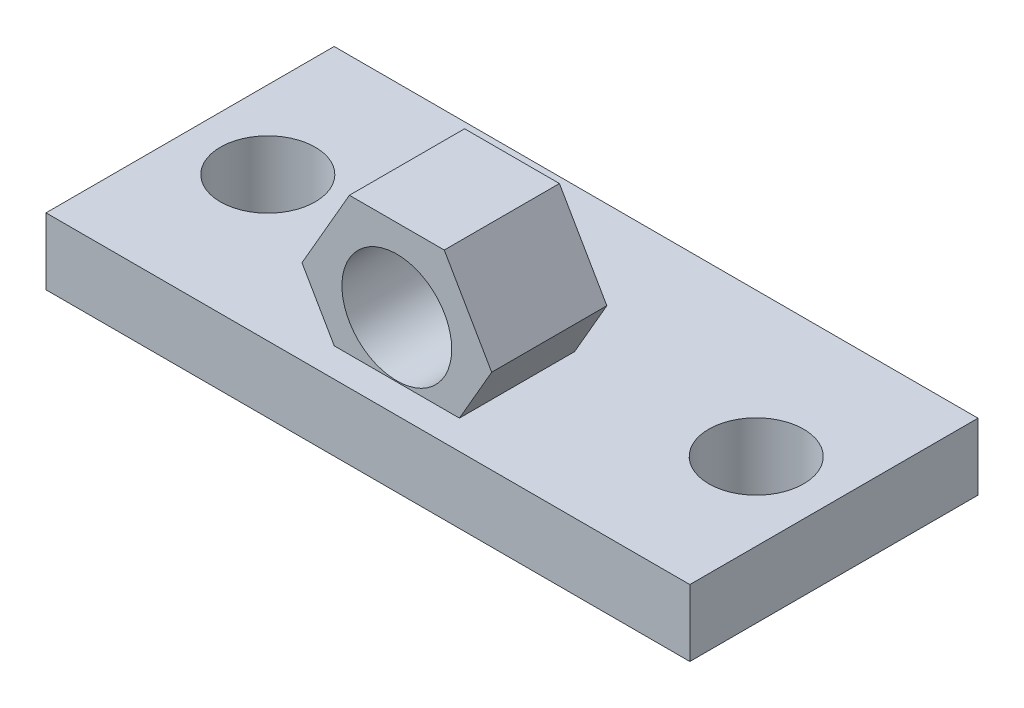
SolidWorks part; units mm, degrees
ref_plane "Alzado" through (0, 0, 0) normal (0, 0, 1) x (1, 0, 0)
ref_plane "Planta" through (0, 0, 0) normal (0, 1, 0) x (1, 0, 0)
ref_plane "Vista lateral" through (0, 0, 0) normal (1, 0, 0) x (0, 0, -1)
sketch "Croquis1" plane through (0, 0, 0) normal (0, 1, 0) x (1, 0, 0)
  line L1 (-24.1402, 10.804) -> (24.1402, 10.804)
  line L2 (-24.1402, 10.804) -> (-24.1402, -10.804)
  line L3 (-24.1402, -10.804) -> (24.1402, -10.804)
  line L4 (24.1402, 10.804) -> (24.1402, -10.804)
  line L5 (-24.1402, 10.804) -> (24.1402, -10.804) construction
  line L6 (-24.1402, -10.804) -> (24.1402, 10.804) construction
  point P0 (0, 0)
extrude "Saliente-Extruir1" add sketch "Croquis1" along normal blind 5
sketch "Croquis2" plane through (0, 0, 0) normal (0, 1, 0) x (1, 0, 0)
  line L0 (0, 6.8714) -> (0, -4.9266)
  circle A0 centre (-18.3128, 0) radius 2.9742
  circle A1 centre (18.3128, 0) radius 2.9742
extrude "Cortar-Extruir1" cut sketch "Croquis2" along normal blind 15 and the other way blind 23 contours A1 | A0
sketch "Croquis3" plane through (0, 0, 0) normal (0, 1, 0) x (1, 0, 0)
  circle A0 centre (18.3128, 0) radius 3.556
  dimension "D1" = 7.112
extrude "Cortar-Extruir2" cut sketch "Croquis3" along normal blind 31.496 and the other way blind 20.828
sketch "Croquis4" plane through (0, 5, 0) normal (0, 1, 0) x (1, 0, 0)
  circle A0 centre (-18.3128, 0) radius 3.556
  dimension "D1" = 7.112
extrude "Cortar-Extruir3" cut sketch "Croquis4" along normal blind 8.636 and the other way blind 20.828
sketch "Croquis5" plane through (0, 0, 0) normal (0, 0, 1) x (1, 0, 0)
  line L0 (0, -7.1779) -> (0, 14.9058) construction
  line L2 (7.1123, 9.1901) -> (3.5561, 15.3495)
  line L3 (3.5561, 15.3495) -> (-3.5561, 15.3495)
  line L4 (-3.5561, 15.3495) -> (-7.1123, 9.1901)
  line L5 (-7.1123, 9.1901) -> (-3.5561, 3.0307)
  line L6 (-3.5561, 3.0307) -> (3.5561, 3.0307)
  line L7 (3.5561, 3.0307) -> (7.1123, 9.1901)
  circle A0 centre (0, 9.1901) radius 4.1173
  circle A1 centre (0, 9.1901) radius 6.1594 construction
extrude "Saliente-Extruir2" add sketch "Croquis5" along normal blind 8.636
